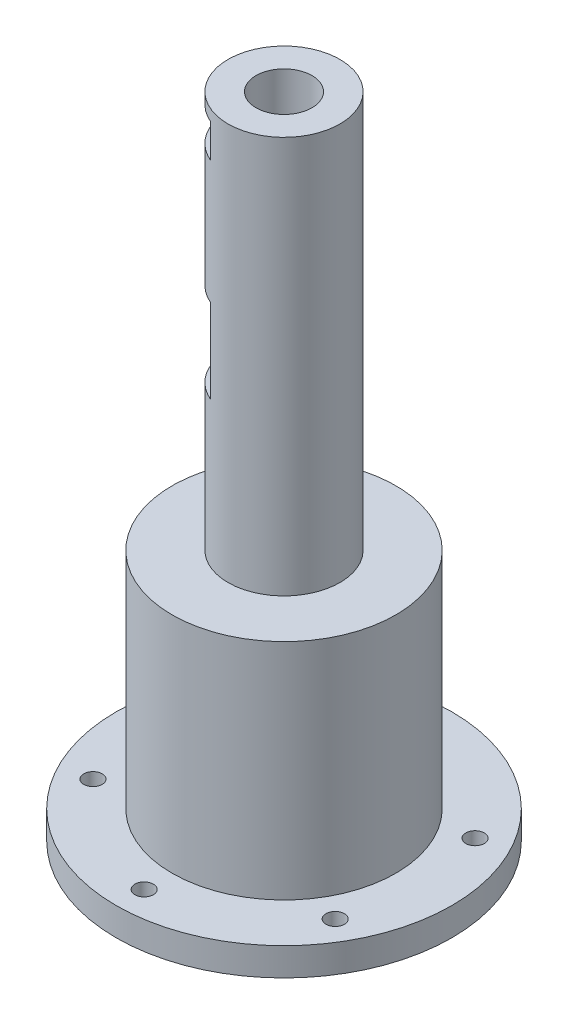
SolidWorks part; units mm, degrees
ref_plane "정면" through (0, 0, 0) normal (0, 0, 1) x (1, 0, 0)
ref_plane "윗면" through (0, 0, 0) normal (0, 1, 0) x (1, 0, 0)
ref_plane "우측면" through (0, 0, 0) normal (1, 0, 0) x (0, 0, -1)
sketch "스케치1" plane through (0, 0, 0) normal (0, 1, 0) x (1, 0, 0)
  circle A0 centre (0, 0) radius 30
  dimension "D1" = 60
extrude "보스-돌출1" add sketch "스케치1" along normal blind 5
sketch "스케치2" plane through (0, 5, 0) normal (0, 1, 0) x (1, 0, 0)
  circle A0 centre (0, 0) radius 20
  dimension "D1" = 40
extrude "보스-돌출2" add sketch "스케치2" along normal blind 40
sketch "스케치4" plane through (0, 5, 0) normal (0, 1, 0) x (1, 0, 0)
  line L0 (0, 0) -> (0, 50000) construction
  line L1 (0, 0) -> (50000, 0) construction
  circle A0 centre (0, 25) radius 2
  circle A6 centre (21.6506, 12.5) radius 2
  circle A7 centre (21.6506, -12.5) radius 2
  circle A8 centre (0, -25) radius 2
  circle A9 centre (-21.6506, -12.5) radius 2
  circle A10 centre (-21.6506, 12.5) radius 2
  point P21 (0, 0)
  dimension "D1" = 4
  dimension "D2" = 25
  dimension "D3" = 6
sketch "스케치5" plane through (0, 45, 0) normal (0, 1, 0) x (1, 0, 0)
  circle A0 centre (0, 0) radius 10
  dimension "D1" = 20
extrude "보스-돌출3" add sketch "스케치5" along normal blind 71 contours A0
sketch "스케치6" plane through (0, 116, 0) normal (0, 1, 0) x (1, 0, 0)
  circle A0 centre (0, 0) radius 5
  dimension "D1" = 10
extrude "컷-돌출2" cut sketch "스케치6" against normal up to next
ref_plane "평면1" through (0, 0, -10) normal (0, 0, -1) x (-1, 0, 0)
sketch "스케치7" plane through (0, 0, -10) normal (0, 0, -1) x (-1, 0, 0)
  line L0 (10, 116) -> (-10, 116) construction
  line L1 (-7.5, 86) -> (7.5, 86)
  line L2 (-7.5, 86) -> (-7.5, 71)
  line L3 (-7.5, 71) -> (7.5, 71)
  line L4 (7.5, 86) -> (7.5, 71)
  line L5 (0, 0) -> (0, 50000) construction
  dimension "D1" = 15
  dimension "D2" = 15
  dimension "D3" = 30
  dimension "D4" = 7.5
extrude "컷-돌출3" cut sketch "스케치7" against normal blind 2
ref_plane "평면2" through (-8.6603, 0, 5) normal (-0.866, 0, 0.5) x (0, -1, 0)
sketch "스케치8" plane through (-8.6603, 0, 5) normal (-0.866, 0, 0.5) x (0, -1, 0)
  line L0 (0, 0) -> (-50000, 0) construction
  line L1 (-116, 10) -> (-116, -10) construction
  line L2 (-86, 7.5) -> (-71, 7.5)
  line L3 (-86, 7.5) -> (-86, -7.5)
  line L4 (-86, -7.5) -> (-71, -7.5)
  line L5 (-71, 7.5) -> (-71, -7.5)
  dimension "D1" = 15
  dimension "D2" = 15
  dimension "D3" = 7.5
  dimension "D4" = 30
extrude "컷-돌출4" cut sketch "스케치8" against normal blind 2
hole_wizard "M4 나사 구멍2" positions "스케치12" profile "스케치13" tap size "M4" standard "ISO" end condition up to next
sketch "스케치12" plane through (0, 5, 0) normal (0, 1, 0) x (1, 0, 0)
  point P0 (0, 25)
  point P3 (21.6506, 12.5)
  point P6 (21.6506, -12.5)
  point P10 (-21.6506, 12.5)
  point P13 (-21.6506, -12.5)
  point P16 (0, -25)
sketch "스케치13" plane through (0, 5, -25) normal (1, 0, 0) x (0, 0, 1)
  line L0 (0, 0) -> (0, 5)
  line L1 (0, 5) -> (1.65, 5)
  line L2 (1.65, 5) -> (1.65, 0)
  line L5 (1.65, 0) -> (0, 0)
  line L11 (0, -6.35) -> (0, 107.95) construction
  dimension "관통 탭 드릴 지름" = 3.3
  dimension "관통 탭 드릴 깊이" = 5
cosmetic thread "구멍 나사산1" parameters "D2"=4
cosmetic thread "구멍 나사산2" parameters "D2"=4
cosmetic thread "구멍 나사산3" parameters "D2"=4
cosmetic thread "구멍 나사산4" parameters "D2"=4
cosmetic thread "구멍 나사산5" parameters "D2"=4
cosmetic thread "구멍 나사산6" parameters "D2"=4
sketch "스케치21" plane through (-8.6603, 0, 5) normal (-0.866, 0, 0.5) x (0, -1, 0)
  line L0 (-116, 10) -> (-116, -10) construction
  line L1 (-114, 7.5) -> (-108, 7.5)
  line L2 (-114, 7.5) -> (-114, -7.5)
  line L3 (-114, -7.5) -> (-108, -7.5)
  line L4 (-108, 7.5) -> (-108, -7.5)
  line L5 (-114, 7.5) -> (-108, -7.5) construction
  line L6 (-114, -7.5) -> (-108, 7.5) construction
  point P0 (-111, 0)
  dimension "D1" = 5
  dimension "D2" = 15
  dimension "D3" = 6
extrude "컷-돌출5" cut sketch "스케치21" against normal blind 2
sketch "스케치22" plane through (0, 0, -10) normal (0, 0, -1) x (-1, 0, 0)
  line L0 (10, 116) -> (-10, 116) construction
  line L1 (-6.8766, 114) -> (8.1234, 114)
  line L2 (-6.8766, 114) -> (-6.8766, 108)
  line L3 (-6.8766, 108) -> (8.1234, 108)
  line L4 (8.1234, 114) -> (8.1234, 108)
  line L5 (-6.8766, 114) -> (8.1234, 108) construction
  line L6 (-6.8766, 108) -> (8.1234, 114) construction
  point P0 (0.6234, 111)
  dimension "D1" = 15
  dimension "D2" = 6
  dimension "D3" = 5
extrude "컷-돌출6" cut sketch "스케치22" against normal blind 2
